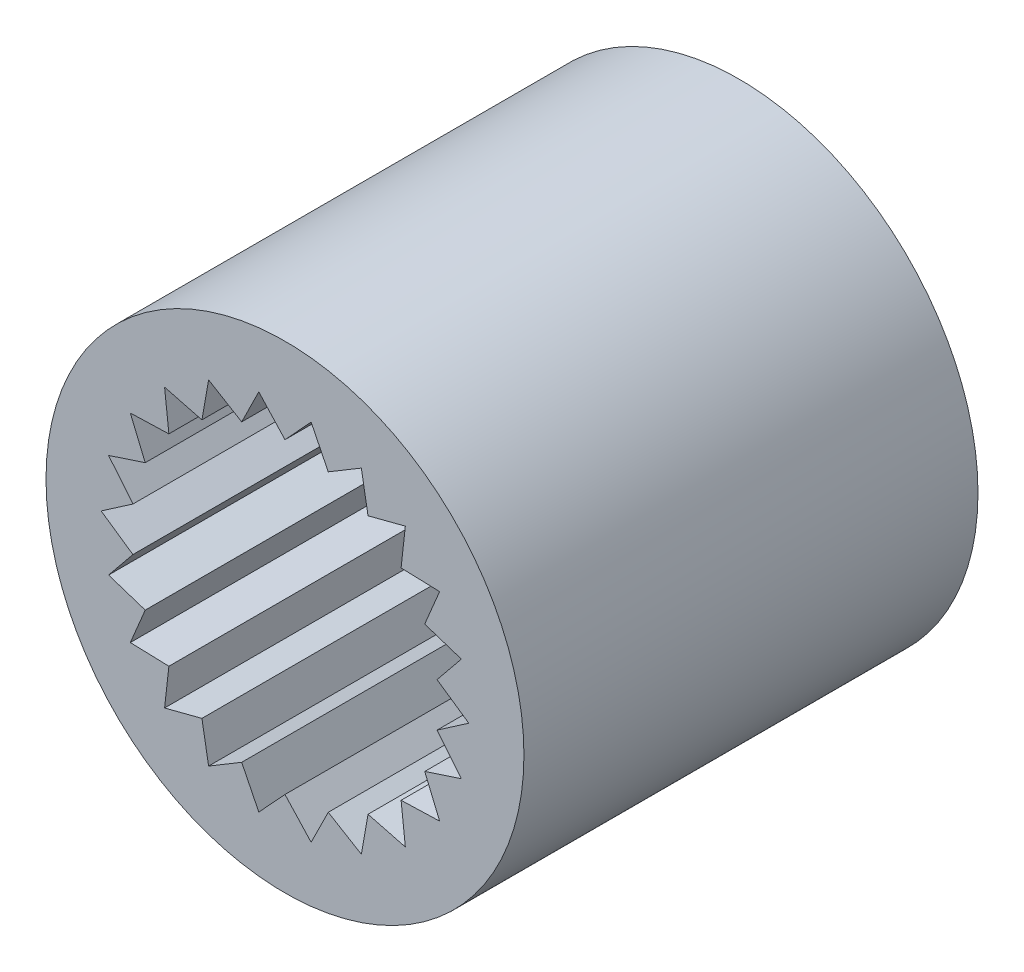
SolidWorks part; units mm, degrees
ref_plane "Front Plane" through (0, 0, 0) normal (0, 0, 1) x (1, 0, 0)
ref_plane "Top Plane" through (0, 0, 0) normal (0, 1, 0) x (1, 0, 0)
ref_plane "Right Plane" through (0, 0, 0) normal (1, 0, 0) x (0, 0, -1)
sketch "Sketch1" plane through (0, 0, 0) normal (0, 1, 0) x (1, 0, 0)
  line L0 (3.5, 0) -> (0, 0)
  line L1 (0, 0) -> (0, -6.65)
  line L2 (0, -6.65) -> (3.5, -6.65)
  line L3 (3.5, -6.65) -> (3.5, 0)
  line L4 (0, 0) -> (0, -6.65) construction
  dimension "D1" = 3.5
  dimension "D2" = 6.65
revolve "Revolve1" add sketch "Sketch1" angle 360 about L4
ref_plane "Plane1" through (0, 0, 0) normal (0, 0, -1) x (-1, 0, 0)
sketch "Sketch2" plane through (0, 0, 0) normal (0, 0, -1) x (-1, 0, 0)
  line L0 (-1.9, 14.1) -> (-2.75, 2.1651)
  line L1 (2.75, 2.1651) -> (1.9, 14.1)
  arc A0 (1.9, 14.1) -> (-1.9, 14.1) centre (0, 14.1) ccw
  arc A1 (-2.75, 2.1651) -> (2.75, 2.1651) centre (0, 0) cw
extrude "Boss-Extrude1" [suppressed] add sketch "Sketch2" against normal blind 1.5
sketch "Sketch3" plane through (0, 0, 6.65) normal (0, 0, 1) x (1, 0, 0)
  line L0 (2.0603, 1.3241) -> (1.7004, 1.4734)
  line L1 (1.7004, 1.4734) -> (1.6038, 1.8509)
  line L2 (1.6038, 1.8509) -> (1.2164, 1.8928)
  line L3 (1.2164, 1.8928) -> (1.0174, 2.2278)
  line L4 (1.0174, 2.2278) -> (0.6339, 2.1589)
  line L5 (0.6339, 2.1589) -> (0.3485, 2.4241)
  line L6 (0.3485, 2.4241) -> (0, 2.25)
  line L7 (0, 2.25) -> (-0.3485, 2.4241)
  line L8 (-0.3485, 2.4241) -> (-0.6339, 2.1589)
  line L9 (-0.6339, 2.1589) -> (-1.0174, 2.2278)
  line L10 (-1.0174, 2.2278) -> (-1.2164, 1.8928)
  line L11 (-1.2164, 1.8928) -> (-1.6038, 1.8509)
  line L12 (-1.6038, 1.8509) -> (-1.7004, 1.4734)
  line L13 (-1.7004, 1.4734) -> (-2.0603, 1.3241)
  line L14 (-2.0603, 1.3241) -> (-2.0467, 0.9347)
  line L15 (-2.0467, 0.9347) -> (-2.3499, 0.69)
  line L16 (-2.3499, 0.69) -> (-2.2271, 0.3202)
  line L17 (-2.2271, 0.3202) -> (-2.4491, 0)
  line L18 (-2.4491, 0) -> (-2.2271, -0.3202)
  line L19 (-2.2271, -0.3202) -> (-2.3499, -0.69)
  line L20 (-2.3499, -0.69) -> (-2.0467, -0.9347)
  line L21 (-2.0467, -0.9347) -> (-2.0603, -1.3241)
  line L22 (-2.0603, -1.3241) -> (-1.7004, -1.4734)
  line L23 (-1.7004, -1.4734) -> (-1.6038, -1.8509)
  line L24 (-1.6038, -1.8509) -> (-1.2164, -1.8928)
  line L25 (-1.2164, -1.8928) -> (-1.0174, -2.2278)
  line L26 (-1.0174, -2.2278) -> (-0.6339, -2.1589)
  line L27 (-0.6339, -2.1589) -> (-0.3485, -2.4241)
  line L28 (-0.3485, -2.4241) -> (0, -2.25)
  line L29 (0, -2.25) -> (0.3485, -2.4241)
  line L30 (0.3485, -2.4241) -> (0.6339, -2.1589)
  line L31 (0.6339, -2.1589) -> (1.0174, -2.2278)
  line L32 (1.0174, -2.2278) -> (1.2164, -1.8928)
  line L33 (1.2164, -1.8928) -> (1.6038, -1.8509)
  line L34 (1.6038, -1.8509) -> (1.7004, -1.4734)
  line L35 (1.7004, -1.4734) -> (2.0603, -1.3241)
  line L36 (2.0603, -1.3241) -> (2.0467, -0.9347)
  line L37 (2.0467, -0.9347) -> (2.3499, -0.69)
  line L38 (2.3499, -0.69) -> (2.2271, -0.3202)
  line L39 (2.2271, -0.3202) -> (2.4491, 0)
  line L40 (2.4491, 0) -> (2.2271, 0.3202)
  line L41 (2.2271, 0.3202) -> (2.3499, 0.69)
  line L42 (2.3499, 0.69) -> (2.0467, 0.9347)
  line L43 (2.0467, 0.9347) -> (2.0603, 1.3241)
extrude "Cut-Extrude1" cut sketch "Sketch3" against normal blind 9
hole_wizard "Ø0.9 (0.9) Diameter Hole1" [suppressed] positions "Sketch5" profile "Sketch4" hole size "Ø0.9" standard "ANSI Metric"
sketch "Sketch5" plane through (0, 0, 0) normal (0, 0, -1) x (-1, 0, 0)
  point P0 (0, 10.6)
  point P1 (0, 12.7)
  point P2 (0, 14.8)
  point P3 (0, 6.4)
  point P4 (0, 8.5)
  point P5 (0, 4.3)
sketch "Sketch4" plane through (0, 10.6, 0) normal (1, 0, 0) x (0, 1, 0)
  line L0 (0, 0) -> (0, 5.6687)
  line L1 (0, 5.6687) -> (0.45, 5.6687)
  line L2 (0.45, 5.6687) -> (0.45, 0)
  line L5 (0.45, 0) -> (0, 0)
  line L11 (0, -6.35) -> (0, 107.95) construction
  dimension "Thru Hole Dia." = 0.9
  dimension "Thru Hole Depth" = 5.6687
sketch "Sketch8" plane through (0, 0, 6.65) normal (0, 0, 1) x (1, 0, 0)
  circle A1 centre (0, 0) radius 3.5
  circle A2 centre (0, 0) radius 3.5
  dimension "D1" = 0
extrude "Cut-Extrude2" [suppressed] cut sketch "Sketch8" against normal blind 10 flip side to cut
sketch "Sketch9" plane through (0, 0, 6.65) normal (0, 0, 1) x (1, 0, 0)
  line L132 (0, -2.25) -> (0.3832, -2.665)
  line L133 (0.3832, -2.665) -> (0.6339, -2.1589)
  line L134 (0.6339, -2.1589) -> (1.1185, -2.4491)
  line L135 (1.1185, -2.4491) -> (1.2164, -1.8928)
  line L136 (1.2164, -1.8928) -> (1.7632, -2.0348)
  line L137 (1.7632, -2.0348) -> (1.7004, -1.4734)
  line L138 (1.7004, -1.4734) -> (2.265, -1.4556)
  line L139 (2.265, -1.4556) -> (2.0467, -0.9347)
  line L140 (2.0467, -0.9347) -> (2.5834, -0.7585)
  line L141 (2.5834, -0.7585) -> (2.2271, -0.3202)
  line L142 (2.2271, -0.3202) -> (2.6924, 0)
  line L143 (2.6924, 0) -> (2.2271, 0.3202)
  line L144 (2.2271, 0.3202) -> (2.5834, 0.7585)
  line L145 (2.5834, 0.7585) -> (2.0467, 0.9347)
  line L146 (2.0467, 0.9347) -> (2.265, 1.4556)
  line L147 (2.265, 1.4556) -> (1.7004, 1.4734)
  line L148 (1.7004, 1.4734) -> (1.7632, 2.0348)
  line L149 (1.7632, 2.0348) -> (1.2164, 1.8928)
  line L150 (1.2164, 1.8928) -> (1.1185, 2.4491)
  line L151 (1.1185, 2.4491) -> (0.6339, 2.1589)
  line L152 (0.6339, 2.1589) -> (0.3832, 2.665)
  line L153 (0.3832, 2.665) -> (0, 2.25)
  line L154 (0, 2.25) -> (-0.3832, 2.665)
  line L155 (-0.3832, 2.665) -> (-0.6339, 2.1589)
  line L156 (-0.6339, 2.1589) -> (-1.1185, 2.4491)
  line L157 (-1.1185, 2.4491) -> (-1.2164, 1.8928)
  line L158 (-1.2164, 1.8928) -> (-1.7632, 2.0348)
  line L159 (-1.7632, 2.0348) -> (-1.7004, 1.4734)
  line L160 (-1.7004, 1.4734) -> (-2.265, 1.4556)
  line L161 (-2.265, 1.4556) -> (-2.0467, 0.9347)
  line L162 (-2.0467, 0.9347) -> (-2.5834, 0.7585)
  line L163 (-2.5834, 0.7585) -> (-2.2271, 0.3202)
  line L164 (-2.2271, 0.3202) -> (-2.6924, 0)
  line L165 (-2.6924, 0) -> (-2.2271, -0.3202)
  line L166 (-2.2271, -0.3202) -> (-2.5834, -0.7585)
  line L167 (-2.5834, -0.7585) -> (-2.0467, -0.9347)
  line L168 (-2.0467, -0.9347) -> (-2.265, -1.4556)
  line L169 (-2.265, -1.4556) -> (-1.7004, -1.4734)
  line L170 (-1.7004, -1.4734) -> (-1.7632, -2.0348)
  line L171 (-1.7632, -2.0348) -> (-1.2164, -1.8928)
  line L172 (-1.2164, -1.8928) -> (-1.1185, -2.4491)
  line L173 (-1.1185, -2.4491) -> (-0.6339, -2.1589)
  line L174 (-0.6339, -2.1589) -> (-0.3832, -2.665)
  line L175 (-0.3832, -2.665) -> (0, -2.25)
  point P0 (-2.0467, 0.8123)
  point P2 (0, 0)
  point P88 (0, 0)
extrude "Cut-Extrude3" cut sketch "Sketch9" against normal blind 10
